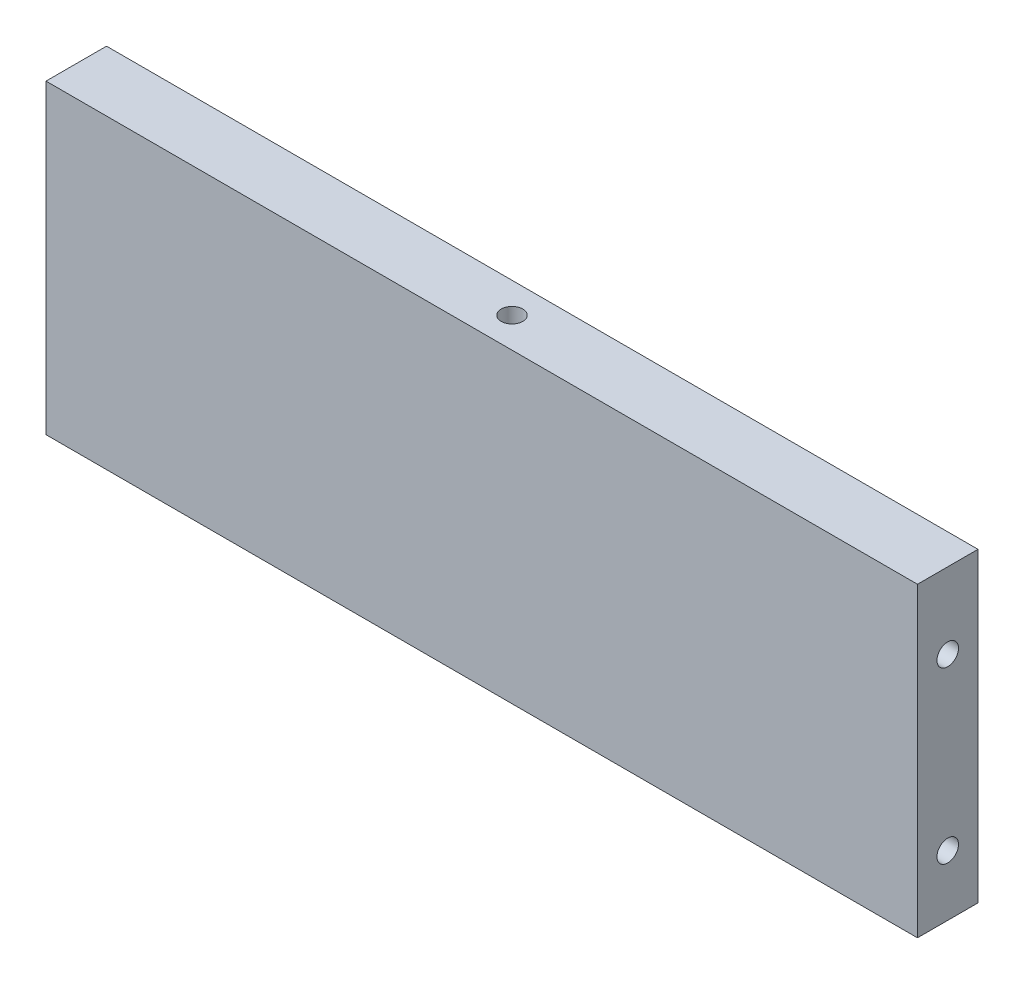
SolidWorks part; units mm, degrees
ref_plane "Front Plane" through (0, 0, 0) normal (0, 0, 1) x (1, 0, 0)
ref_plane "Top Plane" through (0, 0, 0) normal (0, 1, 0) x (1, 0, 0)
ref_plane "Right Plane" through (0, 0, 0) normal (1, 0, 0) x (0, 0, -1)
sketch "Sketch1" plane through (0, 0, 0) normal (0, 1, 0) x (1, 0, 0)
  line L1 (-91.44, -6.35) -> (0, -6.35)
  line L2 (-91.44, -6.35) -> (-91.44, 0)
  line L3 (-91.44, 0) -> (0, 0)
  line L4 (0, -6.35) -> (0, 0)
  point P0 (0, 0)
  dimension "D1" = 6.35
  dimension "D2" = 91.44
extrude "Boss-Extrude1" add sketch "Sketch1" along normal blind 32.131
sketch "Sketch2" plane through (0, 0, 0) normal (1, 0, 0) x (0, 0, -1)
  line L0 (0, 32.131) -> (0, 0) construction
  line L2 (0, 16.0655) -> (-6.35, 16.0655) construction
  line L3 (-6.35, 32.131) -> (-6.35, 0) construction
  circle A0 centre (-3.175, 24.1808) radius 1.1303
  circle A1 centre (-3.175, 6.35) radius 2.2696 construction
  circle A2 centre (-3.175, 24.1808) radius 3.3633 construction
  circle A3 centre (-3.175, 6.35) radius 1.1303
  dimension "D3" = 2.2606
  dimension "D2" = 2.2606
  dimension "D1" = 3.175
extrude "Cut-Extrude1" cut sketch "Sketch2" against normal blind 12.7
ref_plane "Plane1" through (-45.72, 0, 0) normal (1, 0, 0) x (0, 0, -1)
mirror "Mirror2" about plane through (-45.72, 0, 0) normal (1, 0, 0) of "Cut-Extrude1"
sketch "Sketch3" plane through (0, 32.131, 0) normal (0, 1, 0) x (1, 0, 0)
  line L0 (-45.72, -3.4925) -> (-45.72, 3.4925) construction
  line L1 (-91.44, -6.35) -> (0, -6.35) construction
  circle A0 centre (-45.72, -3.175) radius 1.1303
  dimension "D1" = 2.2606
  dimension "D2" = 3.175
extrude "Cut-Extrude2" cut sketch "Sketch3" against normal blind 12.7
